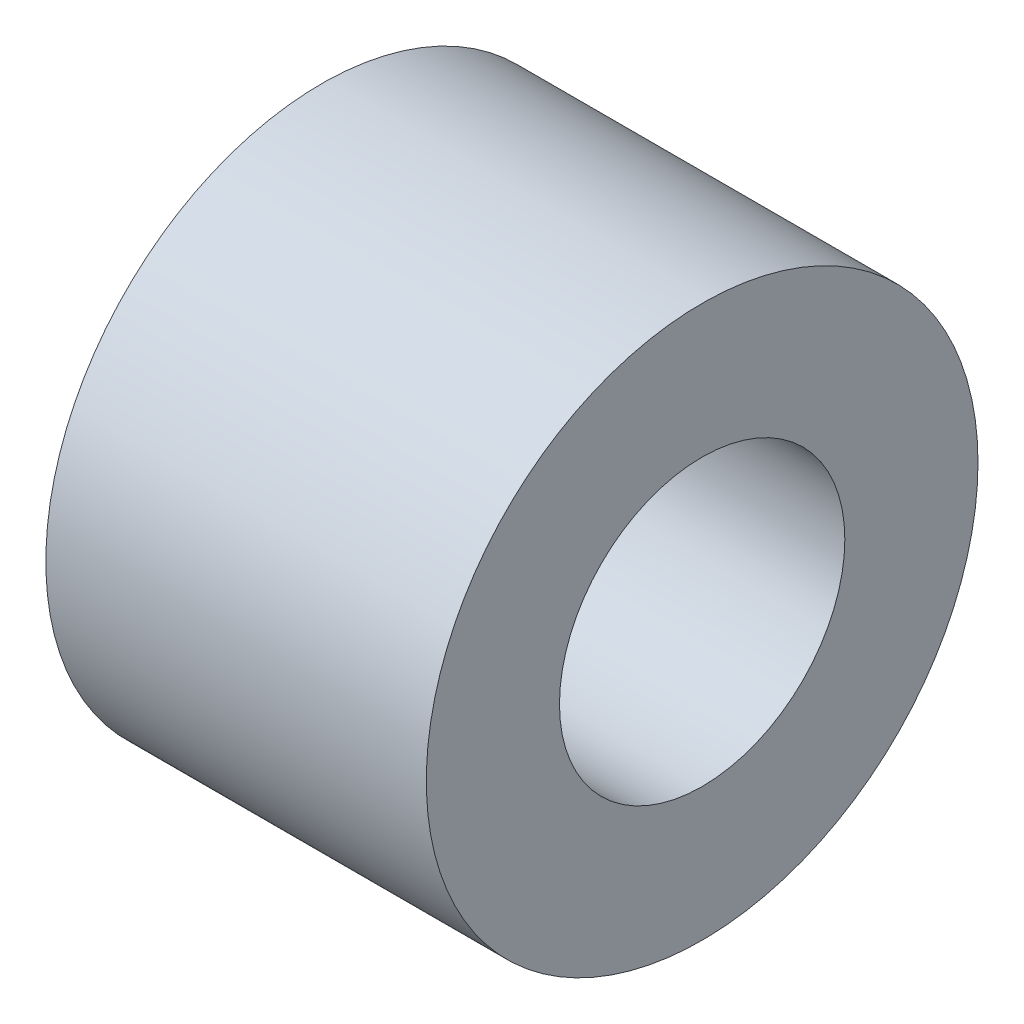
SolidWorks part; units mm, degrees
ref_plane "Plan de face" through (0, 0, 0) normal (0, 0, 1) x (1, 0, 0)
ref_plane "Plan de dessus" through (0, 0, 0) normal (0, 1, 0) x (1, 0, 0)
ref_plane "Plan de droite" through (0, 0, 0) normal (1, 0, 0) x (0, 0, -1)
sketch "Esquisse1" plane through (0, 0, 0) normal (1, 0, 0) x (0, 0, -1)
  circle A0 centre (0, 0) radius 2.9
  circle A1 centre (0, 0) radius 1.5
extrude "Extrusion1" add sketch "Esquisse1" along normal blind 4
